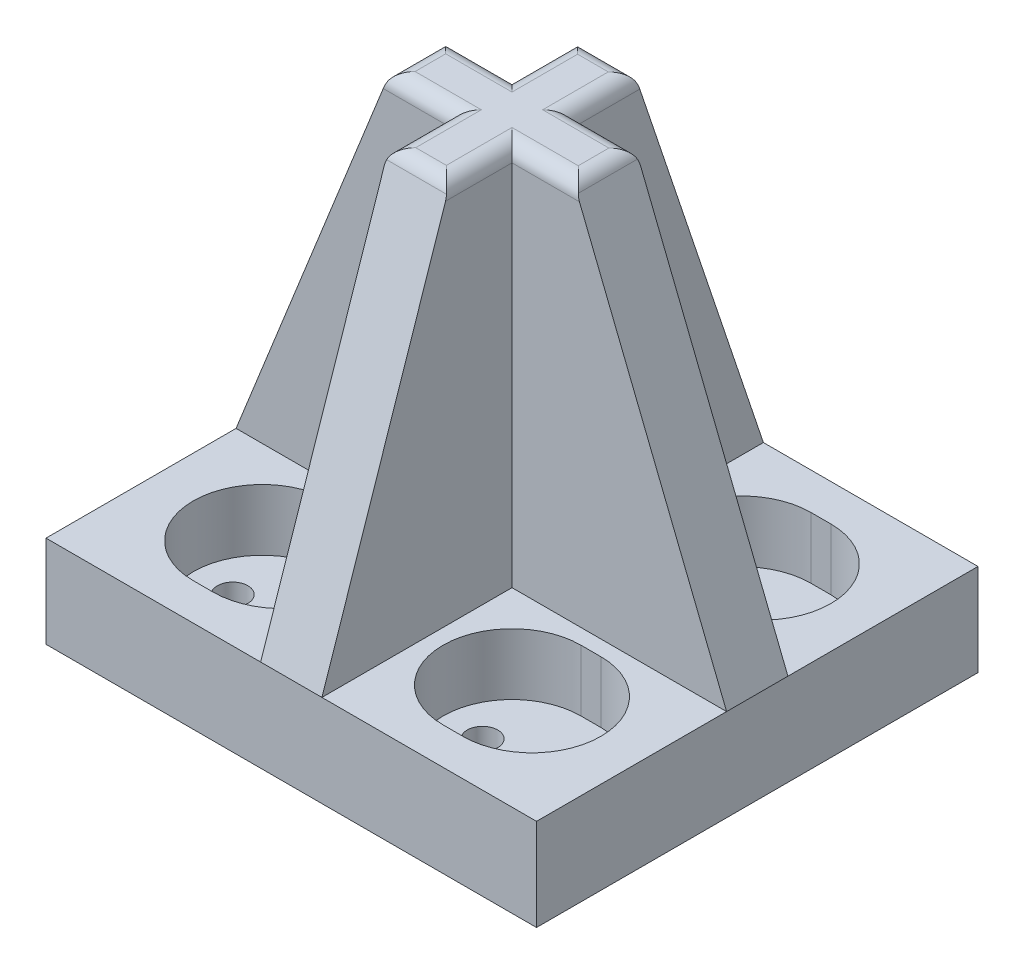
SolidWorks part; units mm, degrees
ref_plane "Front Plane" through (0, 0, 0) normal (0, 0, 1) x (1, 0, 0)
ref_plane "Top Plane" through (0, 0, 0) normal (0, 1, 0) x (1, 0, 0)
ref_plane "Right Plane" through (0, 0, 0) normal (1, 0, 0) x (0, 0, -1)
sketch "Sketch1" plane through (0, 0, 0) normal (0, 1, 0) x (1, 0, 0)
  line L0 (0, 5.2815) -> (0, -7.9343) construction
  line L1 (0, 0) -> (8, 0)
  line L2 (0, 0) -> (0, -7.2)
  line L3 (0, -7.2) -> (8, -7.2)
  line L4 (8, 0) -> (8, -7.2)
  line L5 (10.0956, 0) -> (-11.6883, 0) construction
  dimension "D1" = 8
  dimension "D2" = 7.2
extrude "Boss-Extrude1" add sketch "Sketch1" along normal blind 3
sketch "Sketch2" plane through (0, 3, 0) normal (0, 1, 0) x (1, 0, 0)
  line L0 (3.75, -3.75) -> (4.4, -3.75) construction
  line L1 (3.75, -1.5) -> (4.4, -1.5)
  line L2 (3.75, -6) -> (4.4, -6)
  line L5 (1, 0) -> (1, -7.2) construction
  line L6 (0, -7.2) -> (8, -7.2) construction
  line L7 (0, -1) -> (8, -1) construction
  line L8 (0, 0) -> (0, -7.2) construction
  line L9 (8, -7.2) -> (8, 0) construction
  line L10 (8, 0) -> (0, 0) construction
  arc A0 (3.75, -1.5) -> (3.75, -6) centre (3.75, -3.75) ccw
  arc A1 (4.4, -6) -> (4.4, -1.5) centre (4.4, -3.75) ccw
  point P2 (4.075, -3.75)
  point P7 (1.5, -3.75)
  point P8 (6.65, -3.75)
  point P29 (0, 0)
  point P32 (0, 0)
  dimension "D1" = 4.5
  dimension "D2" = 1
  dimension "D3" = 5.15
  dimension "D4" = 1
  dimension "D5" = 0.5
  dimension "D6" = 0.5
extrude "Cut-Extrude1" cut sketch "Sketch2" against normal blind 2
sketch "Sketch3" plane through (0, 1, 0) normal (0, 1, 0) x (1, 0, 0)
  line L0 (1.5, -3.75) -> (4.075, -3.75) construction
  line L1 (4.075, -1.5) -> (4.075, -6) construction
  line L2 (4.4, -1.5) -> (3.75, -1.5) construction
  line L3 (3.75, -6) -> (4.4, -6) construction
  arc A0 (3.75, -1.5) -> (3.75, -6) centre (3.75, -3.75) ccw construction
  circle A2 centre (2.7875, -3.75) radius 0.4981
  circle A3 centre (5.3625, -3.75) radius 0.4981
  point P1 (2.7875, -3.75)
  point P16 (0, 0)
  point P17 (3.7239, -5.25)
  point P18 (0, 0)
  dimension "D1" = 0.9962
extrude "Cut-Extrude2" cut sketch "Sketch3" against normal through all
sketch "Sketch4" plane through (0, 0, 0) normal (-1, 0, 0) x (0, 0, 1)
  line L0 (0, 3) -> (0, 15.5)
  line L1 (0, 15.5) -> (3, 15.5)
  line L2 (3, 15.5) -> (7.2, 3)
  line L3 (0, 3) -> (7.2, 3) construction
  line L4 (0, 3) -> (7.2, 3)
  dimension "D1" = 12.5
  dimension "D2" = 3
extrude "Boss-Extrude2" add sketch "Sketch4" against normal blind 1
sketch "Sketch7" plane through (0, 0, 0) normal (0, 0, -1) x (-1, 0, 0)
  line L0 (0, 15.5) -> (-3, 15.5)
  line L1 (-3, 15.5) -> (-8, 3)
  line L3 (0, 15.5) -> (0, 0) construction
  line L4 (-8, 3) -> (0, 3)
  line L5 (0, 3) -> (0, 15.5)
  dimension "D1" = 3
extrude "Boss-Extrude3" add sketch "Sketch7" against normal blind 1
mirror "Mirror16" about plane through (0, 3, 0) normal (1, 0, 0) of "Cut-Extrude2", "Cut-Extrude1", "Boss-Extrude3", "Boss-Extrude2", "Boss-Extrude1"
mirror "Mirror21" about plane through (0, 3, 0) normal (0, 0, 1) of "Boss-Extrude2", "Boss-Extrude3", "Cut-Extrude2", "Boss-Extrude1", "Cut-Extrude1"
mirror "Mirror22" about plane through (0, 3, 0) normal (-1, 0, 0) of "Mirror21", "Boss-Extrude1", "Cut-Extrude1", "Cut-Extrude2"
fillet "Fillet6" radius 0.5 12 edges at (-3, 15.5, 0) (-2, 15.5, -1) (-1, 15.5, -2) (0, 15.5, -3) (1, 15.5, -2) (2, 15.5, -1) (3, 15.5, 0) (2, 15.5, 1) (1, 15.5, 2) (0, 15.5, 3) (-1, 15.5, 2) (-2, 15.5, 1)
